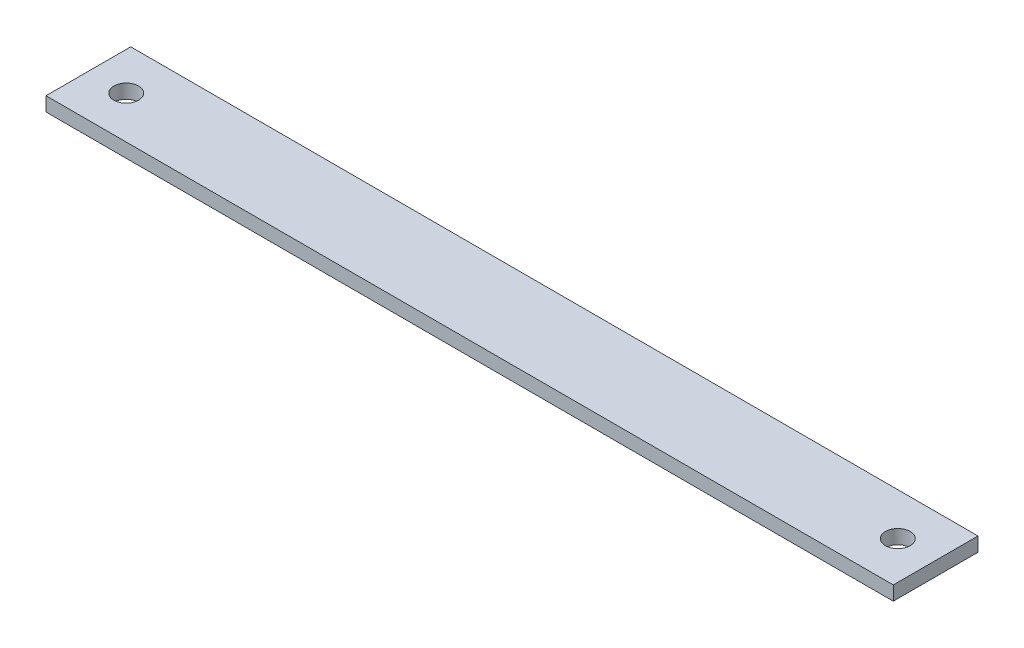
SolidWorks part; units mm, degrees
ref_plane "Front Plane" through (0, 0, 0) normal (0, 0, 1) x (1, 0, 0)
ref_plane "Top Plane" through (0, 0, 0) normal (0, 1, 0) x (1, 0, 0)
ref_plane "Right Plane" through (0, 0, 0) normal (1, 0, 0) x (0, 0, -1)
sketch "Sketch1" plane through (0, 0, 0) normal (0, 1, 0) x (1, 0, 0)
  line L1 (-56.2708, 60.9647) -> (705.7292, 60.9647)
  line L2 (-56.2708, 60.9647) -> (-56.2708, -15.2353)
  line L3 (-56.2708, -15.2353) -> (705.7292, -15.2353)
  line L4 (705.7292, 60.9647) -> (705.7292, -15.2353)
  dimension "D1" = 76.2
  dimension "D2" = 762
extrude "Boss-Extrude1" add sketch "Sketch1" along normal blind 12.7
ref_plane "Plane1" through (705.7292, 12.7, 15.2353) normal (1, 0, 0) x (0, 0, -1)
sketch "Sketch4" plane through (0, 12.7, 0) normal (0, 1, 0) x (1, 0, 0)
  line L0 (324.7292, -15.2353) -> (324.7292, 60.9647) construction
  line L1 (-56.2708, -15.2353) -> (705.7292, -15.2353) construction
  line L2 (705.7292, 60.9647) -> (-56.2708, 60.9647) construction
  line L5 (-56.2708, 22.8647) -> (705.7292, 22.8647) construction
  line L6 (-56.2708, 60.9647) -> (-56.2708, -15.2353) construction
  line L7 (705.7292, -15.2353) -> (705.7292, 60.9647) construction
  circle A0 centre (671.6932, 22.8647) radius 11.1125
  circle A1 centre (-22.2348, 22.8647) radius 11.1125
  dimension "D1" = 22.225
  dimension "D2" = 34.036
extrude "Cut-Extrude1" cut sketch "Sketch4" against normal through all
